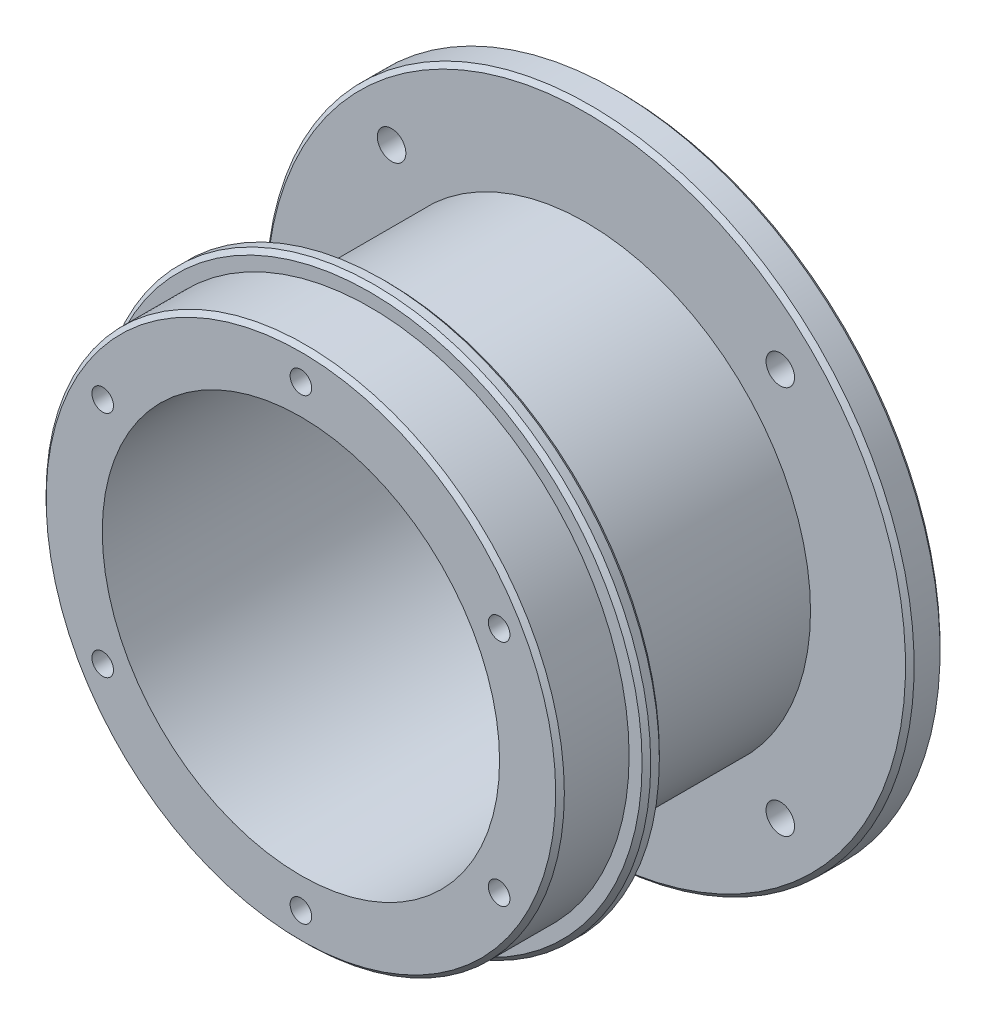
SolidWorks part; units mm, degrees
material "6061 合金"
ref_plane "前视基准面" through (0, 0, 0) normal (0, 0, 1) x (1, 0, 0)
ref_plane "上视基准面" through (0, 0, 0) normal (0, 1, 0) x (1, 0, 0)
ref_plane "右视基准面" through (0, 0, 0) normal (1, 0, 0) x (0, 0, -1)
sketch "草图1" plane through (0, 0, 0) normal (0, 0, 1) x (1, 0, 0)
  circle A1 centre (0, 0) radius 32
  dimension "D1" = 64
extrude "凸台-拉伸1" add sketch "草图1" along normal blind 2
sketch "草图2" plane through (0, 0, 2) normal (0, 0, 1) x (1, 0, 0)
  circle A0 centre (0, 0) radius 30
  dimension "D1" = 60
extrude "凸台-拉伸2" add sketch "草图2" along normal blind 8
sketch "草图3" plane through (0, 0, 0) normal (0, 0, -1) x (-1, 0, 0)
  circle A0 centre (0, 0) radius 23
  dimension "D1" = 46
extrude "切除-拉伸1" cut sketch "草图3" against normal through all
sketch "草图4" plane through (0, 0, 0) normal (0, 0, -1) x (-1, 0, 0)
  circle A0 centre (0, 0) radius 23
  circle A1 centre (0, 0) radius 26
  circle A2 centre (0, 0) radius 23 construction
  dimension "D1" = 52
extrude "凸台-拉伸3" add sketch "草图4" along normal blind 23
sketch "草图5" plane through (0, 0, -23) normal (0, 0, -1) x (-1, 0, 0)
  line L0 (-22.5, 22.5) -> (-22.5, 20.6409) construction
  line L1 (22.5, 22.5) -> (-22.5, 22.5) construction
  line L2 (22.5, 22.5) -> (22.5, -22.5) construction
  line L3 (22.5, -22.5) -> (-22.5, -22.5) construction
  line L4 (-22.5, 22.5) -> (-22.5, -22.5) construction
  line L5 (22.5, 22.5) -> (-22.5, -22.5) construction
  line L6 (22.5, -22.5) -> (-22.5, 22.5) construction
  line L11 (30, 30) -> (-30, -30) construction
  line L12 (30, -30) -> (-30, 30) construction
  circle A0 centre (22.5, 22.5) radius 1.75
  circle A1 centre (-22.5, 22.5) radius 1.75
  circle A2 centre (-22.5, -22.5) radius 1.75
  circle A3 centre (22.5, -22.5) radius 1.75
  circle A4 centre (0, 0) radius 23
  circle A5 centre (0, 0) radius 37.5
  circle A6 centre (0, 0) radius 23 construction
  point P0 (0, 0)
  point P5 (0, 0)
  circle M11 centre (0, 0) radius 26
  circle M12 centre (0, 0) radius 23
  dimension "D4" = 3.5
  dimension "D6" = 75
  dimension "D1" = 45
  dimension "D2" = 45
  dimension "D3" = 60
extrude "凸台-拉伸4" add sketch "草图5" along normal blind 4 contours A5 A0 A1 A2 A3 M11 | A0 | A1 | A2 | A3 | M11 M12
sketch "草图14" plane through (0, 0, -27) normal (0, 0, -1) x (-1, 0, 0)
  circle A1 centre (22.5, -22.5) radius 1.75
  circle A2 centre (22.5, -22.5) radius 1.75 construction
  circle A3 centre (-22.5, -22.5) radius 1.75
  circle A4 centre (-22.5, -22.5) radius 1.75 construction
  circle A5 centre (-22.5, 22.5) radius 1.75
  circle A6 centre (-22.5, 22.5) radius 1.75 construction
  circle A7 centre (22.5, 22.5) radius 1.75
  circle A8 centre (22.5, 22.5) radius 1.75 construction
  point P1 (22.5, -22.5)
  point P14 (22.5, 22.5)
  point P15 (-22.5, -22.5)
  point P16 (-22.5, 22.5)
  dimension "D1" = 0
  dimension "D2" = 0
  dimension "D3" = 0
  dimension "D4" = 0
hole_wizard "M4 螺纹孔3" positions "3D草图5" profile "草图15" tap size "M4" standard "GB"
sketch3d "3D草图5"
  point P0 (-22.5, -22.5, -27)
  point P3 (-22.5, 22.5, -27)
  point P6 (22.5, -22.5, -27)
  point P9 (22.5, 22.5, -27)
sketch "草图15" plane through (-22.5, -22.5, -27) normal (1, 0, 0) x (0, 1, 0)
  line L0 (0, 0) -> (0, 9.0914)
  line L1 (0, 9.0914) -> (1.65, 8.1)
  line L2 (1.65, 8.1) -> (1.65, 0)
  line L5 (1.65, 0) -> (0, 0)
  line L10 (0, 9.0914) -> (-1.65, 8.1) construction
  line L11 (0, -6.35) -> (0, 107.95) construction
  dimension "螺纹孔钻头直径" = 3.3
  dimension "螺纹孔钻头深度" = 8.1
  dimension "导头角度" = 118
cosmetic thread "孔螺蚊线9" parameters "D1"=4, "D2"=4
cosmetic thread "孔螺蚊线10" parameters "D1"=4, "D2"=4
cosmetic thread "孔螺蚊线11" parameters "D1"=4, "D2"=4
cosmetic thread "孔螺蚊线12" parameters "D1"=4, "D2"=4
chamfer "倒角1" distance 0.5 angle 45 1 edges at (32, 0, 0)
sketch "草图16" plane through (0, 0, 10) normal (0, 0, 1) x (1, 0, 0)
  circle A0 centre (0, 0) radius 26.5 construction
  point P3 (0, -26.5)
  point P6 (-22.9497, -13.25)
  point P7 (-22.9497, 13.25)
  point P8 (0, 26.5)
  point P9 (22.9497, 13.25)
  point P10 (22.9497, -13.25)
  point P11 (0, 0)
  dimension "D1" = 53
  dimension "D2" = 6
hole_wizard "M3 螺纹孔1" positions "3D草图6" profile "草图17" tap size "M3" standard "GB"
sketch3d "3D草图6"
  point P0 (0, -26.5, 10)
  point P3 (22.9497, -13.25, 10)
  point P6 (22.9497, 13.25, 10)
  point P9 (0, 26.5, 10)
  point P12 (-22.9497, 13.25, 10)
  point P15 (-22.9497, -13.25, 10)
sketch "草图17" plane through (0, -26.5, 10) normal (1, 0, 0) x (0, -1, 0)
  line L0 (0, 0) -> (0, 6.7511)
  line L1 (0, 6.7511) -> (1.25, 6)
  line L2 (1.25, 6) -> (1.25, 0)
  line L5 (1.25, 0) -> (0, 0)
  line L10 (0, 6.7511) -> (-1.25, 6) construction
  line L11 (0, -6.35) -> (0, 107.95) construction
  dimension "螺纹孔钻头直径" = 2.5
  dimension "螺纹孔钻头深度" = 6
  dimension "导头角度" = 118
cosmetic thread "孔螺蚊线13" parameters "D1"=6, "D2"=3
cosmetic thread "孔螺蚊线14" parameters "D1"=6, "D2"=3
cosmetic thread "孔螺蚊线15" parameters "D1"=6, "D2"=3
cosmetic thread "孔螺蚊线16" parameters "D1"=6, "D2"=3
cosmetic thread "孔螺蚊线17" parameters "D1"=6, "D2"=3
cosmetic thread "孔螺蚊线18" parameters "D1"=6, "D2"=3
chamfer "倒角2" distance 0.5 angle 45 2 edges at (-37.5, 0, -27) (-37.5, 0, -23)
chamfer "倒角3" distance 0.5 angle 45 2 edges at (30, 0, 10) (32, 0, 2)
